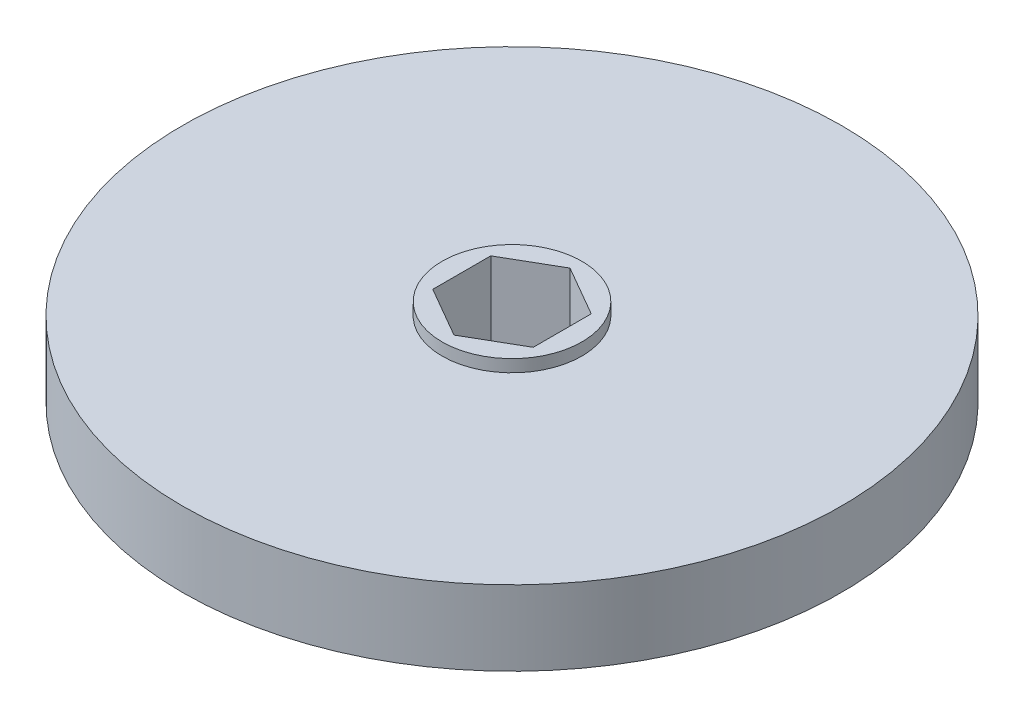
SolidWorks part; units mm, degrees
ref_plane "Front Plane" through (0, 0, 0) normal (0, 0, 1) x (1, 0, 0)
ref_plane "Top Plane" through (0, 0, 0) normal (0, 1, 0) x (1, 0, 0)
ref_plane "Right Plane" through (0, 0, 0) normal (1, 0, 0) x (0, 0, -1)
sketch "Sketch1" plane through (0, 0, 0) normal (0, 1, 0) x (1, 0, 0)
  circle A0 centre (0, 0) radius 41.91
  dimension "D1" = 83.82
extrude "Boss-Extrude1" add sketch "Sketch1" along normal mid plane 9.525
sketch "Sketch2" plane through (0, 0, 0) normal (0, 1, 0) x (1, 0, 0)
  circle A0 centre (0, 0) radius 8.89
  dimension "D1" = 17.78
extrude "Boss-Extrude2" add sketch "Sketch2" along normal mid plane 12.6492
sketch "Sketch3" plane through (0, 6.3246, 0) normal (0, 1, 0) x (1, 0, 0)
  line L0 (0, 0) -> (0, 7.3763) construction
  line L1 (0, 7.3763) -> (-6.3881, 3.6882)
  line L2 (-6.3881, 3.6882) -> (-6.3881, -3.6882)
  line L3 (-6.3881, -3.6882) -> (0, -7.3763)
  line L4 (0, -7.3763) -> (6.3881, -3.6882)
  line L5 (6.3881, -3.6882) -> (6.3881, 3.6882)
  line L6 (6.3881, 3.6882) -> (0, 7.3763)
  circle A0 centre (0, 0) radius 6.3881 construction
  dimension "D1" = 12.7762
extrude "Cut-Extrude1" cut sketch "Sketch3" against normal through all
sketch "Sketch4" plane through (0, 4.7625, 0) normal (0, 1, 0) x (1, 0, 0)
  circle A0 centre (0, 0) radius 40.64
  dimension "D1" = 81.28
